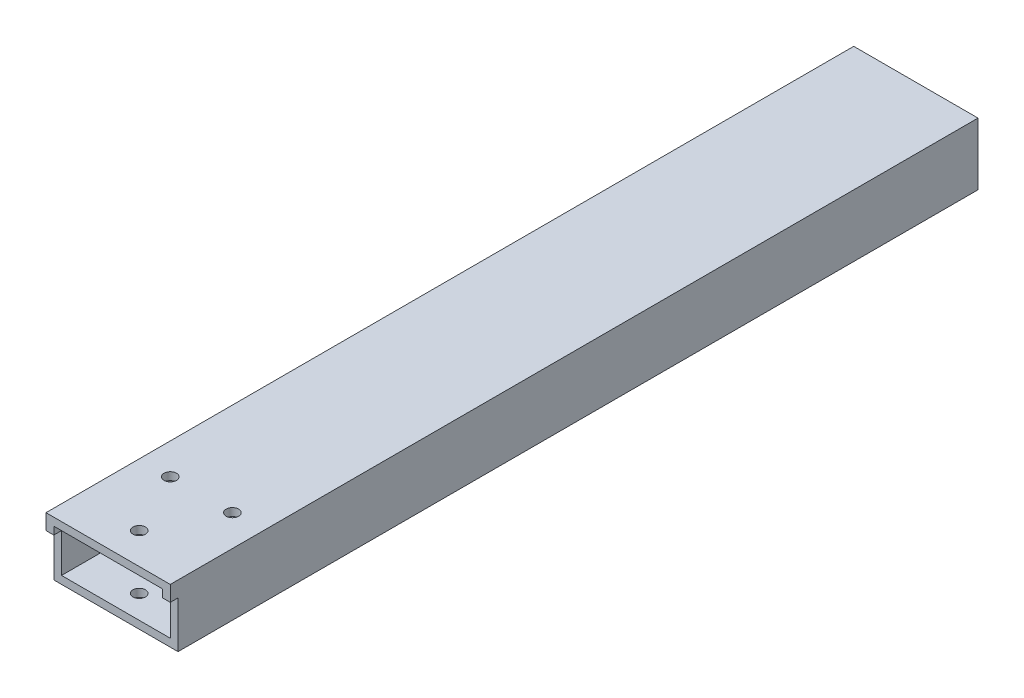
SolidWorks part; units mm, degrees
ref_plane "Front Plane" through (0, 0, 0) normal (0, 0, 1) x (1, 0, 0)
ref_plane "Top Plane" through (0, 0, 0) normal (0, 1, 0) x (1, 0, 0)
ref_plane "Right Plane" through (0, 0, 0) normal (1, 0, 0) x (0, 0, -1)
sketch "Sketch1" plane through (0, 0, 0) normal (0, 0, 1) x (1, 0, 0)
  line L0 (3.175, 3.175) -> (47.625, 3.175)
  line L1 (0, 0) -> (50.8, 0)
  line L2 (0, 0) -> (0, 25.4)
  line L3 (0, 25.4) -> (50.8, 25.4)
  line L4 (50.8, 0) -> (50.8, 25.4)
  line L5 (47.625, 3.175) -> (47.625, 22.225)
  line L6 (3.175, 22.225) -> (47.625, 22.225)
  line L7 (3.175, 3.175) -> (3.175, 22.225)
  dimension "D1" = 50.8
  dimension "D2" = 25.4
  dimension "D3" = 3.175
extrude "Boss-Extrude1" add sketch "Sketch1" along normal blind 330.2
sketch "Sketch2" plane through (0, 0, 330.2) normal (0, 0, 1) x (1, 0, 0)
  line L0 (50.8, 0) -> (50.8, 25.4) construction
  line L1 (0, 0) -> (50.8, 0)
  line L2 (0, 0) -> (0, 19.05)
  line L3 (0, 19.05) -> (50.8, 19.05)
  line L4 (50.8, 0) -> (50.8, 19.05)
  dimension "D1" = 50.8
  dimension "D2" = 19.05
extrude "Cut-Extrude1" cut sketch "Sketch2" against normal blind 3.175
sketch "Sketch3" plane through (0, 25.4, 0) normal (0, 1, 0) x (1, 0, 0)
  line L0 (50.8, -330.2) -> (0, -330.2) construction
  line L1 (12.7, -292.1) -> (38.1, -292.1) construction
  line L2 (25.4, -330.2) -> (25.4, 0) construction
  line L3 (50.8, 0) -> (0, 0) construction
  circle A0 centre (12.7, -292.1) radius 2.5527
  circle A1 centre (38.1, -292.1) radius 2.5527
  circle A2 centre (25.4, -317.5) radius 2.5527
  point P12 (25.4, -292.1)
  dimension "D1" = 5.1054
  dimension "D2" = 5.1054
  dimension "D3" = 5.1054
  dimension "D6" = 25.4
  dimension "D4" = 12.7
  dimension "D5" = 38.1
extrude "Cut-Extrude2" cut sketch "Sketch3" against normal blind 44.45
equation "\"D2@Sketch2\"=1.-.25"
